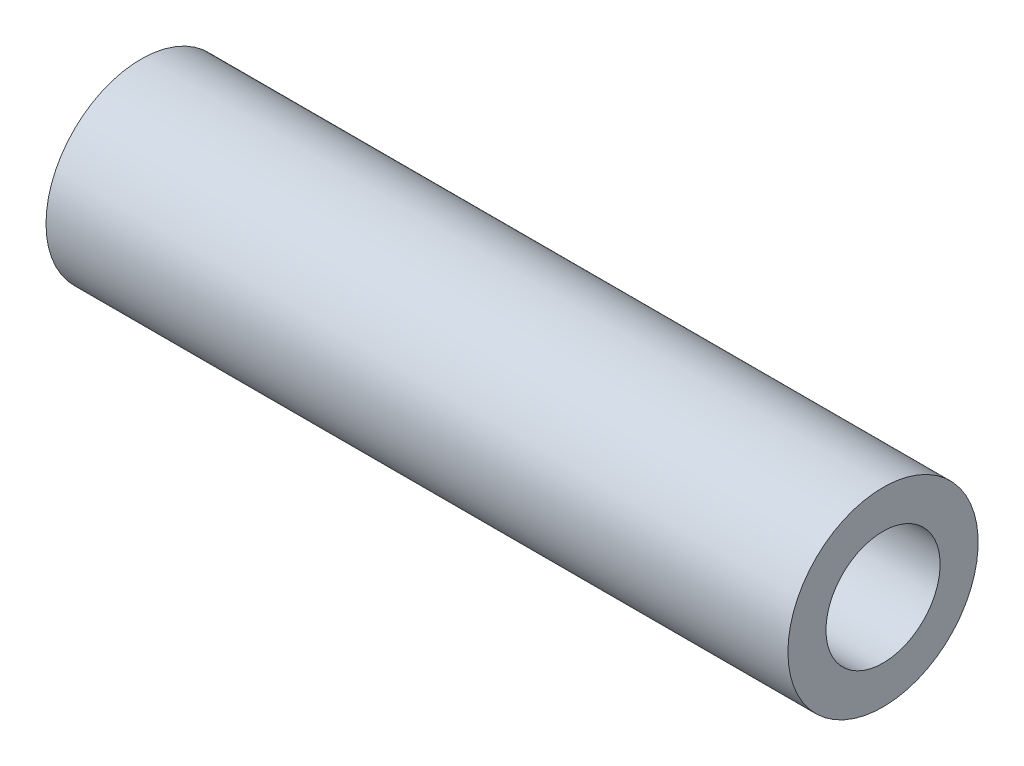
SolidWorks part; units mm, degrees
material "6061 Alloy"
ref_plane "Front Plane" through (0, 0, 0) normal (0, 0, 1) x (1, 0, 0)
ref_plane "Top Plane" through (0, 0, 0) normal (0, 1, 0) x (1, 0, 0)
ref_plane "Right Plane" through (0, 0, 0) normal (1, 0, 0) x (0, 0, -1)
sketch "Sketch1" plane through (0, 0, 0) normal (0, 0, 1) x (1, 0, 0)
  line L0 (0, 0) -> (75.7031, 0) construction
  line L1 (0, 12.7) -> (165.1, 12.7)
  line L2 (0, 12.7) -> (0, 21.1667)
  line L3 (0, 21.1667) -> (165.1, 21.1667)
  line L4 (165.1, 12.7) -> (165.1, 21.1667)
  dimension "D1" = 12.7
  dimension "D2" = 8.4667
  dimension "D3" = 165.1
revolve "Revolve1" add sketch "Sketch1" angle 360 about L0
